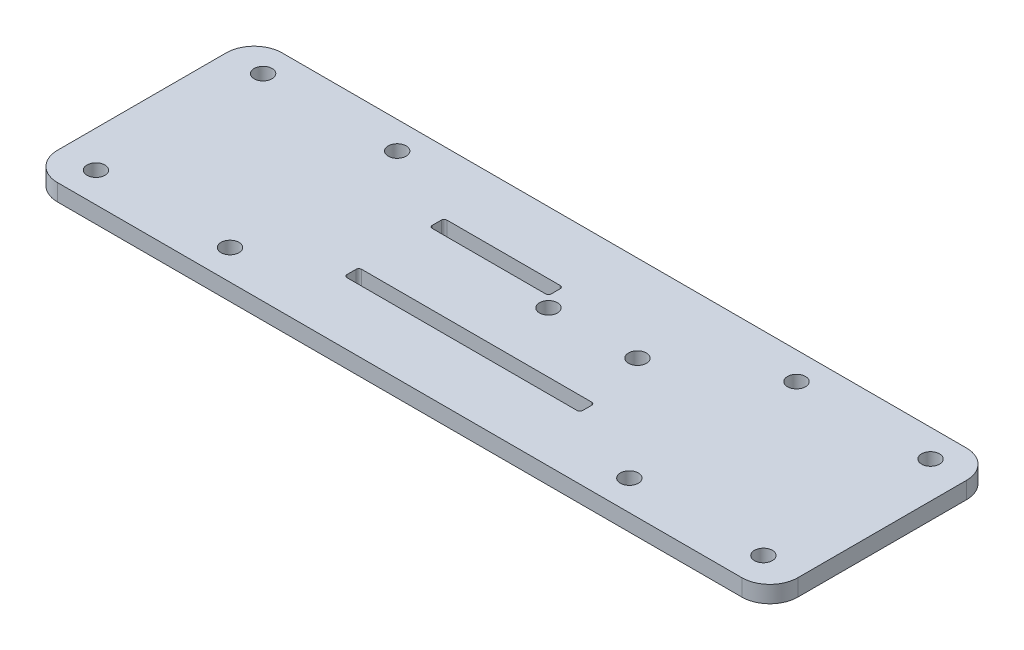
SolidWorks part; units mm, degrees
ref_plane "前视基准面" through (0, 0, 0) normal (0, 0, 1) x (1, 0, 0)
ref_plane "上视基准面" through (0, 0, 0) normal (0, 1, 0) x (1, 0, 0)
ref_plane "右视基准面" through (0, 0, 0) normal (1, 0, 0) x (0, 0, -1)
other "Configuration Table"
sketch "草图1" plane through (0, 0, 0) normal (0, 1, 0) x (1, 0, 0)
  line L0 (-40.8508, 4.523) -> (-40.8508, 14.9172) construction
  line L1 (-106.8508, 24.548) -> (25.1492, 24.548)
  line L2 (-106.8508, 24.548) -> (-106.8508, -15.502)
  line L3 (-106.8508, -15.502) -> (25.1492, -15.502)
  line L4 (25.1492, 24.548) -> (25.1492, -15.502)
  line L5 (-106.8508, 24.548) -> (25.1492, -15.502) construction
  line L6 (-106.8508, -15.502) -> (25.1492, 24.548) construction
  line L7 (-40.8508, 4.523) -> (-53.3439, 4.523) construction
  line L8 (-61.8508, 13.423) -> (-40.6508, 13.423)
  line L9 (-61.8508, 13.423) -> (-61.8508, 10.823)
  line L10 (-61.8508, 10.823) -> (-40.6508, 10.823)
  line L11 (-40.6508, 13.423) -> (-40.6508, 10.823)
  line L12 (-61.8508, 13.423) -> (-40.6508, 10.823) construction
  line L13 (-61.8508, 10.823) -> (-40.6508, 13.423) construction
  line L19 (-61.8508, -1.777) -> (-19.8508, -1.777)
  line L20 (-61.8508, -1.777) -> (-61.8508, -4.377)
  line L21 (-61.8508, -4.377) -> (-19.8508, -4.377)
  line L22 (-19.8508, -1.777) -> (-19.8508, -4.377)
  line L23 (-61.8508, -1.777) -> (-19.8508, -4.377) construction
  line L24 (-61.8508, -4.377) -> (-19.8508, -1.777) construction
  circle A1 centre (18.6492, 19.648) radius 1.6
  circle A2 centre (18.6492, -10.152) radius 1.6
  circle A3 centre (-5.2508, 19.648) radius 1.6
  circle A4 centre (-5.2508, -10.152) radius 1.6
  circle A5 centre (-100.3508, -10.152) radius 1.6
  circle A6 centre (-76.4508, -10.152) radius 1.6
  circle A7 centre (-100.3508, 19.648) radius 1.6
  circle A8 centre (-76.4508, 19.648) radius 1.6
  circle A9 centre (-38.7499, 8.923) radius 1.6
  circle A10 centre (-23.0508, 9.0949) radius 1.6
  point P0 (-40.8508, 4.523)
  point P23 (-51.2508, 12.123)
  point P28 (-61.8508, 12.123)
  point P34 (-40.8508, -3.077)
  point P39 (-19.8508, -3.077)
  dimension "D3" = 4.9
  dimension "D4" = 6.5
  dimension "D5" = 29.8
  dimension "D6" = 23.9
  dimension "D9" = 21.2
  dimension "D16" = 15.7
  dimension "D1" = 132
  dimension "D2" = 40.05
  dimension "D7" = 29.8
  dimension "D8" = 2.6
  dimension "D10" = 6.3
  dimension "D11" = 45
  dimension "D12" = 2.6
  dimension "D13" = 0
  dimension "D14" = 45
  dimension "D15" = 6.3
  dimension "D17" = 13.3
  dimension "D18" = 3.2
extrude "凸台-拉伸1" add sketch "草图1" along normal blind 3
fillet "圆角1" radius 5 1 edges at (25.1492, 1.5, -24.548)
fillet "圆角2" radius 5 3 edges at (-106.8508, 1.5, -24.548) (-106.8508, 1.5, 15.502) (25.1492, 1.5, 15.502)
ref_plane "基准面1" through (-40.8508, 0, 0) normal (1, 0, 0) x (0, 0, -1)
fillet "圆角3" radius 0.5 8 edges at (-19.8508, 1.5, 4.377) (-40.6508, 1.5, -10.823) (-19.8508, 1.5, 1.777) (-40.6508, 1.5, -13.423) (-61.8508, 1.5, 1.777) (-61.8508, 1.5, 4.377) (-61.8508, 1.5, -10.823) (-61.8508, 1.5, -13.423)
